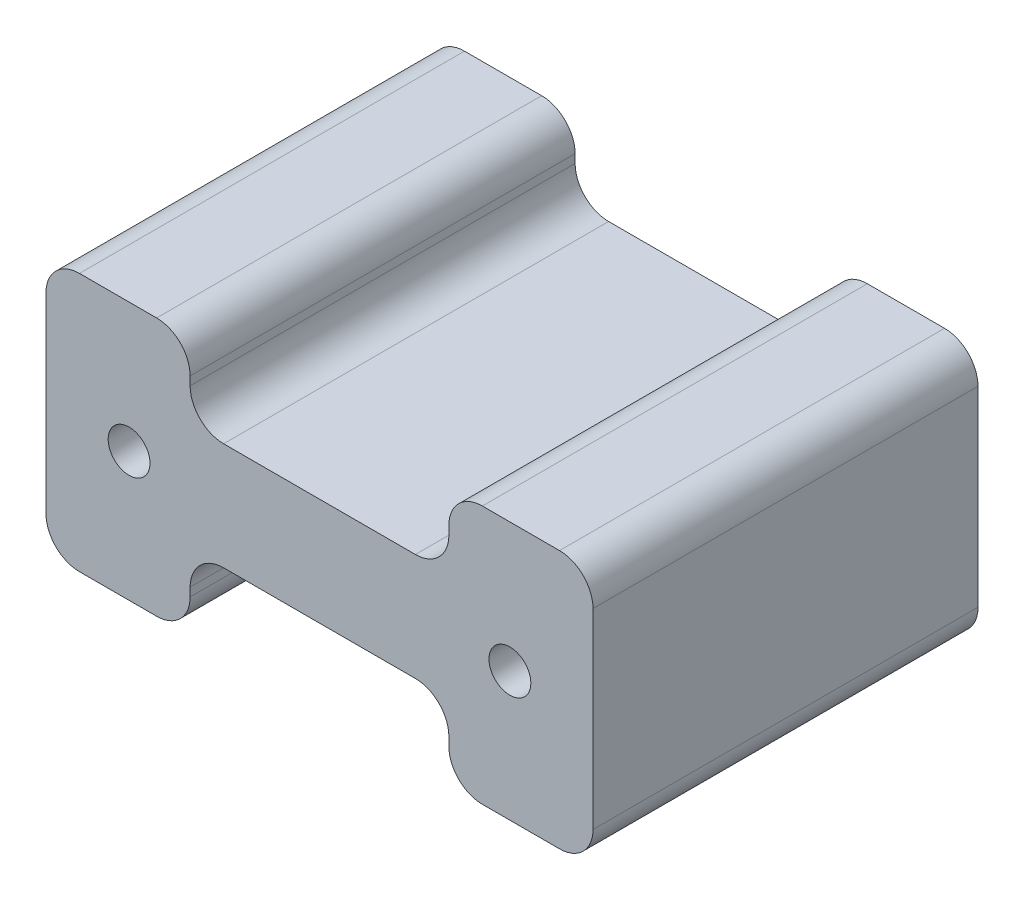
SolidWorks part; units mm, degrees
ref_plane "前视基准面" through (0, 0, 0) normal (0, 0, 1) x (1, 0, 0)
ref_plane "上视基准面" through (0, 0, 0) normal (0, 1, 0) x (1, 0, 0)
ref_plane "右视基准面" through (0, 0, 0) normal (1, 0, 0) x (0, 0, -1)
sketch "草图1" plane through (0, 0, 0) normal (0, 0, 1) x (1, 0, 0)
  line L0 (12.612, 26.3586) -> (-20.0654, 26.3586) construction
  line L2 (-20.0654, 34.0751) -> (12.612, 34.0751)
  line L3 (-20.0654, 34.0751) -> (-20.0654, 18.6421)
  line L4 (-20.0654, 18.6421) -> (12.612, 18.6421)
  line L5 (12.612, 34.0751) -> (12.612, 18.6421)
  line L6 (-20.0654, 34.0751) -> (12.612, 18.6421) construction
  line L7 (-20.0654, 18.6421) -> (12.612, 34.0751) construction
  point P4 (-3.7267, 26.3586)
extrude "凸台-拉伸1" add sketch "草图1" against normal blind 23
sketch "草图2" plane through (0, 0, 0) normal (0, 0, 1) x (1, 0, 0)
  line L0 (-3.7267, 34.0751) -> (-3.7267, 18.6421) construction
  line L1 (4.0024, 14.1336) -> (-11.4558, 14.1336)
  line L2 (4.0024, 29.5665) -> (-11.4558, 29.5665)
  line L3 (12.612, 34.0751) -> (-20.0654, 34.0751) construction
  line L4 (-20.0654, 18.6421) -> (12.612, 18.6421) construction
  line L5 (-3.7267, 26.3586) -> (7.6483, 26.3586) construction
  line L6 (-3.7267, 26.3586) -> (-15.1017, 26.3586) construction
  line L7 (4.0024, 29.5665) -> (4.0024, 38.5836)
  line L8 (4.0024, 38.5836) -> (-11.4558, 38.5836)
  line L9 (-11.4558, 29.5665) -> (-11.4558, 38.5836)
  line L10 (4.0024, 29.5665) -> (-11.4558, 38.5836) construction
  line L11 (4.0024, 38.5836) -> (-11.4558, 29.5665) construction
  line L12 (-11.4558, 23.1506) -> (-11.4558, 14.1336)
  line L13 (4.0024, 23.1506) -> (-11.4558, 23.1506)
  line L14 (4.0024, 23.1506) -> (4.0024, 14.1336)
  line L15 (4.0024, 14.1336) -> (-11.4558, 23.1506) construction
  line L16 (4.0024, 23.1506) -> (-11.4558, 14.1336) construction
  circle A2 centre (-15.1017, 26.3586) radius 1.25
  circle A3 centre (7.6483, 26.3586) radius 1.25
extrude "切除-拉伸1" cut sketch "草图2" against normal through all
fillet "圆角1" radius 2 4 edges at (12.612, 18.6421, -11.5) (12.612, 34.0751, -11.5) (-20.0654, 18.6421, -11.5) (-20.0654, 34.0751, -11.5)
fillet "圆角2" radius 2 8 edges at (-11.4558, 34.0751, -11.5) (4.0024, 34.0751, -11.5) (4.0024, 18.6421, -11.5) (-11.4558, 18.6421, -11.5) (-11.4558, 23.1506, -11.5) (4.0024, 23.1506, -11.5) (4.0024, 29.5665, -11.5) (-11.4558, 29.5665, -11.5)
